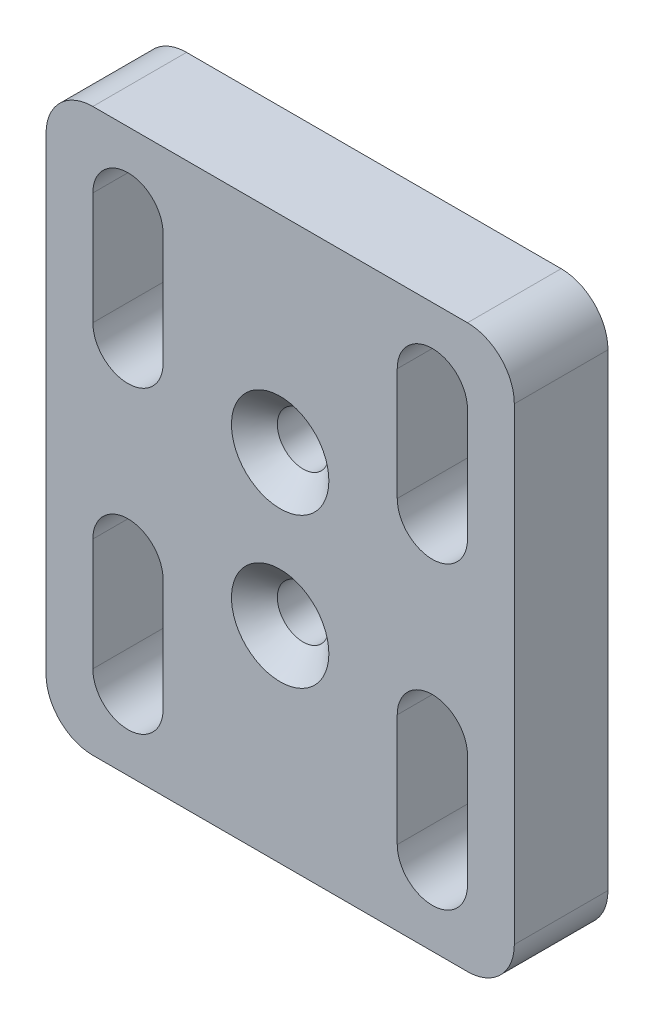
SolidWorks part; units mm, degrees
ref_plane "Front Plane" through (0, 0, 0) normal (0, 0, 1) x (1, 0, 0)
ref_plane "Top Plane" through (0, 0, 0) normal (0, 1, 0) x (1, 0, 0)
ref_plane "Right Plane" through (0, 0, 0) normal (1, 0, 0) x (0, 0, -1)
sketch "Sketch1" plane through (0, 0, 0) normal (0, 0, 1) x (1, 0, 0)
  line L1 (0, 0) -> (50, 0)
  line L2 (0, 0) -> (0, 60)
  line L3 (0, 60) -> (50, 60)
  line L4 (50, 0) -> (50, 60)
  dimension "D1" = 60
  dimension "D2" = 50
extrude "Boss-Extrude1" add sketch "Sketch1" along normal blind 10
sketch "Sketch2" plane through (0, 0, 10) normal (0, 0, 1) x (1, 0, 0)
  line L0 (8.75, 20) -> (8.75, 8) construction
  line L1 (12.5, 20) -> (12.5, 8)
  line L2 (5, 20) -> (5, 8)
  line L3 (0, 0) -> (50, 0) construction
  line L4 (41.25, 40) -> (41.25, 52) construction
  line L5 (37.5, 40) -> (37.5, 52)
  line L6 (45, 40) -> (45, 52)
  line L7 (41.25, 20) -> (41.25, 8) construction
  line L8 (37.5, 20) -> (37.5, 8)
  line L9 (45, 20) -> (45, 8)
  line L11 (0, 60) -> (0, 0) construction
  line L12 (5, 30) -> (50, 30) construction
  line L14 (50, 0) -> (50, 60) construction
  line L16 (8.75, 40) -> (8.75, 52) construction
  line L17 (12.5, 40) -> (12.5, 52)
  line L18 (5, 40) -> (5, 52)
  line L24 (25, 60) -> (25, 0) construction
  line L25 (50, 60) -> (0, 60) construction
  arc A0 (12.5, 20) -> (5, 20) centre (8.75, 20) ccw
  arc A1 (5, 8) -> (12.5, 8) centre (8.75, 8) ccw
  arc A2 (37.5, 40) -> (45, 40) centre (41.25, 40) ccw
  arc A3 (45, 52) -> (37.5, 52) centre (41.25, 52) ccw
  arc A4 (37.5, 20) -> (45, 20) centre (41.25, 20) cw
  arc A5 (45, 8) -> (37.5, 8) centre (41.25, 8) cw
  arc A8 (12.5, 40) -> (5, 40) centre (8.75, 40) cw
  arc A9 (5, 52) -> (12.5, 52) centre (8.75, 52) cw
  point P2 (8.75, 14)
  point P7 (0, 0)
  point P15 (41.25, 46)
  point P21 (41.25, 14)
  point P39 (8.75, 46)
  point P68 (0, 0)
  point P83 (0, 0)
  dimension "D1" = 8
  dimension "D4" = 5
  dimension "D5" = 7.5
fillet "Fillet1" radius 5 4 edges at (50, 0, 5) (0, 0, 5) (0, 60, 5) (50, 60, 5)
extrude "Cut-Extrude1" cut sketch "Sketch2" against normal blind 10
sketch "Sketch3" plane through (0, 0, 10) normal (0, 0, 1) x (1, 0, 0)
  line L0 (25, 60) -> (25, 0) construction
  line L1 (45, 60) -> (5, 60) construction
  line L2 (5, 0) -> (45, 0) construction
  line L3 (0, 30) -> (50, 30) construction
  line L4 (0, 55) -> (0, 5) construction
  line L5 (50, 5) -> (50, 55) construction
  point P0 (25, 38)
  point P1 (25, 22)
  dimension "D1" = 16
hole_wizard "CSK for M5 Countersunk Flat Head1" positions "Sketch4" profile "Sketch5" countersink size "M5" standard "BSI"
sketch "Sketch4" plane through (0, 0, 10) normal (0, 0, 1) x (1, 0, 0)
  point P0 (25, 38)
  point P3 (25, 22)
sketch "Sketch5" plane through (25, 38, 10) normal (1, 0, 0) x (0, -1, 0)
  line L0 (0, 0) -> (0, 31.6524)
  line L1 (0, 31.6524) -> (2.75, 30)
  line L2 (2.75, 30) -> (2.75, 2.45)
  line L3 (2.75, 2.45) -> (5.2, 0)
  line L5 (5.2, 0) -> (0, 0)
  line L6 (-2.75, 2.45) -> (-5.2, 0) construction
  line L10 (0, 31.6524) -> (-2.75, 30) construction
  line L11 (0, -6.35) -> (0, 107.95) construction
  dimension "Hole Dia." = 5.5
  dimension "Hole Depth" = 30
  dimension "Near C'Sink Dia." = 10.4
  dimension "Near C'Sink Angle" = 90
  dimension "Drill Angle" = 118
